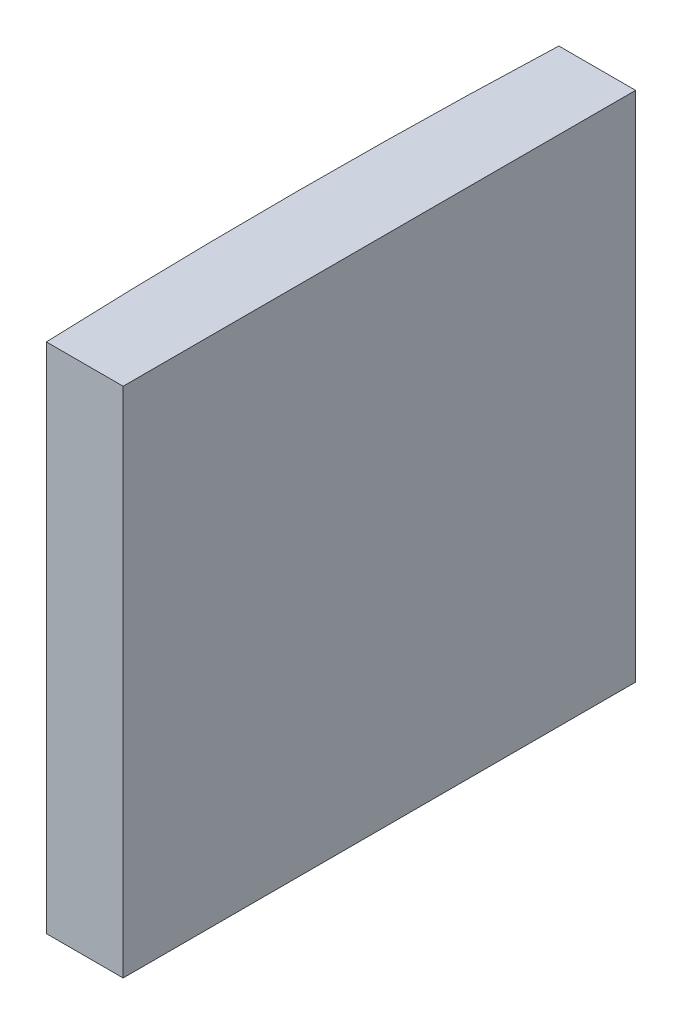
SolidWorks part; units mm, degrees
ref_plane "前视基准面" through (0, 0, 0) normal (0, 0, 1) x (1, 0, 0)
ref_plane "上视基准面" through (0, 0, 0) normal (0, 1, 0) x (1, 0, 0)
ref_plane "右视基准面" through (0, 0, 0) normal (1, 0, 0) x (0, 0, -1)
sketch "草图1" plane through (0, 0, 0) normal (0, 1, 0) x (1, 0, 0)
  line L0 (10.7432, 0) -> (-281.568, 0) construction
  line L1 (-253.9513, 10) -> (-250.9548, 10)
  line L2 (-253.9513, -10) -> (-250.9548, -10)
  line L3 (-250.9548, 10) -> (-250.9548, -10)
  arc A0 (-253.9513, 10) -> (-253.9513, -10) centre (4.3552, 0) ccw
  point P2 (-281.568, 0)
  point P19 (-254.1448, 0)
  point P20 (-250.9548, 0)
  dimension "D2" = 10
  dimension "D3" = 258.5
  dimension "D4" = 3.19
  dimension "D1" = 10
extrude "凸台-拉伸1" add sketch "草图1" along normal blind 20
